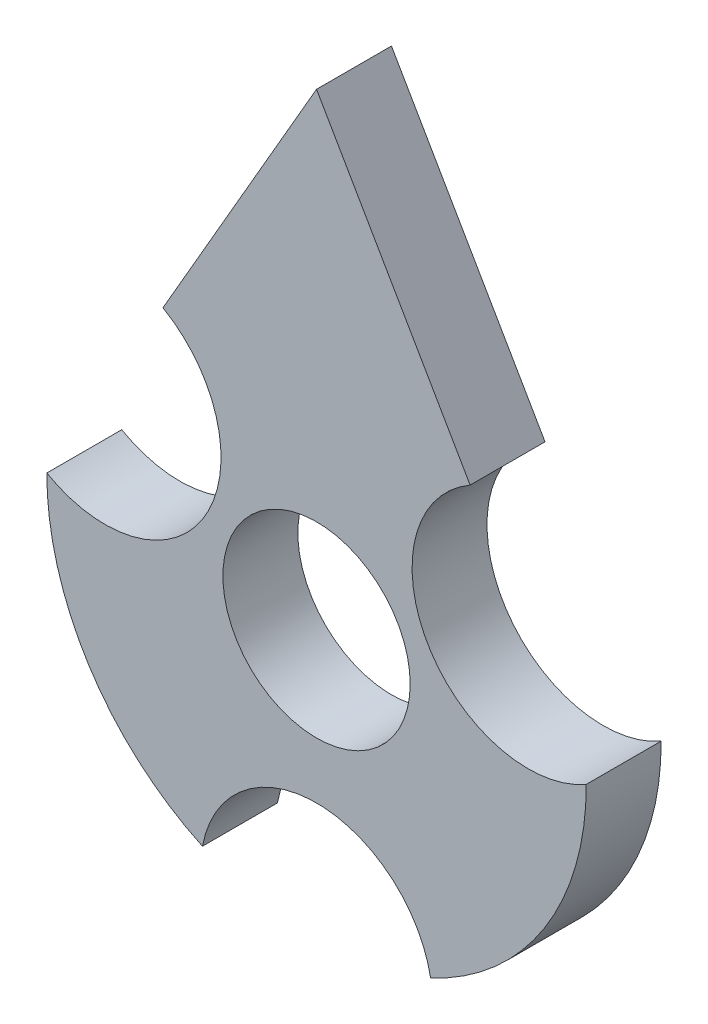
SolidWorks part; units mm, degrees
ref_plane "Front Plane" through (0, 0, 0) normal (0, 0, 1) x (1, 0, 0)
ref_plane "Top Plane" through (0, 0, 0) normal (0, 1, 0) x (1, 0, 0)
ref_plane "Right Plane" through (0, 0, 0) normal (1, 0, 0) x (0, 0, -1)
sketch "Sketch1" plane through (0, 0, 0) normal (0, 0, 1) x (1, 0, 0)
  line L0 (113.8554, 0) -> (-113.8554, 0) construction
  line L1 (0, -83.0741) -> (0, -72) construction
  line L2 (0, 125) -> (0, 217.3893) construction
  line L3 (0, 125) -> (41, 53.9859)
  line L4 (0, 125) -> (-41, 53.9859)
  line L5 (0, -83.0741) -> (0, -286.944) construction
  line L6 (0, -40) -> (0, 72) construction
  line L7 (71.9994, 0.2934) -> (72.1688, 0)
  line L8 (-71.9994, 0.2934) -> (-72.1688, 0)
  circle A0 centre (0, 0) radius 25
  arc A1 (-71.9994, 0.2934) -> (-30.4601, -65.2394) centre (0, 0) ccw
  arc A2 (30.4601, -65.2394) -> (-30.4601, -65.2394) centre (0, -71) ccw
  arc A3 (41, 53.9859) -> (72, 0.2923) centre (56.5, 27.1391) ccw
  arc A4 (-41, 53.9859) -> (-72, 0.2923) centre (-56.5, 27.1391) cw
  arc A6 (30.4601, -65.2394) -> (71.9994, 0.2934) centre (0, 0) ccw
  point P3 (0, 0)
  point P4 (0, 0)
  point P8 (0, 0)
  point P22 (0, 0)
  point P23 (0, 0)
  point P24 (0, 0)
  dimension "D1" = 50
  dimension "D2" = 143
  dimension "D5" = 62
  dimension "D6" = 62
  dimension "D3" = 60
  dimension "D4" = 125
  dimension "D7" = 196
  dimension "D8" = 113
extrude "Boss-Extrude1" add sketch "Sketch1" along normal mid plane 20 contours A2 A6 A3 L3 L4 A4 A1 A0
